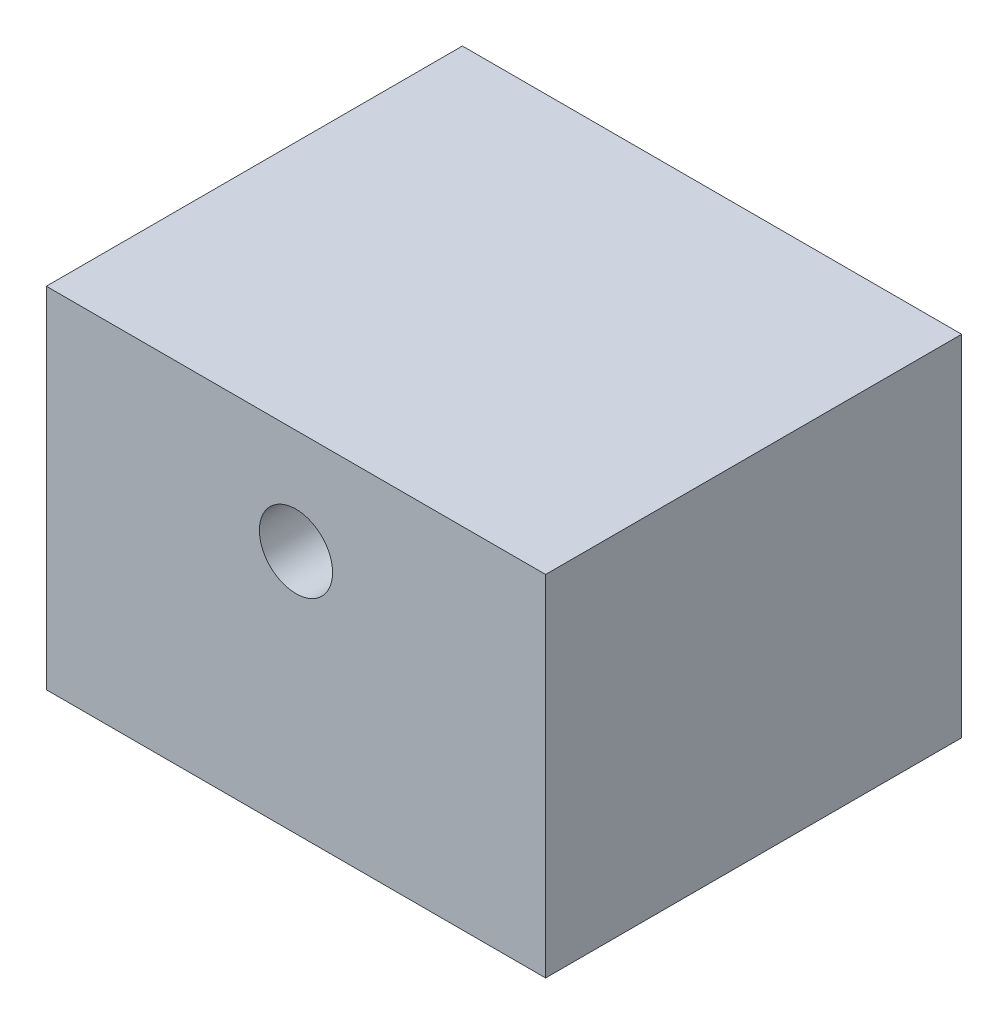
SolidWorks part; units mm, degrees
material "ABS PC"
ref_plane "Front Plane" through (0, 0, 0) normal (0, 0, 1) x (1, 0, 0)
ref_plane "Top Plane" through (0, 0, 0) normal (0, 1, 0) x (1, 0, 0)
ref_plane "Right Plane" through (0, 0, 0) normal (1, 0, 0) x (0, 0, -1)
sketch "Sketch1" plane through (0, 0, 0) normal (0, 0, 1) x (1, 0, 0)
  line L1 (0, 0) -> (30, 0)
  line L2 (0, 0) -> (0, 21)
  line L3 (0, 21) -> (30, 21)
  line L4 (30, 0) -> (30, 21)
  circle A0 centre (15, 14.7) radius 2.2
  point P7 (15, 0)
  dimension "D3" = 4.4
  dimension "D1" = 21
  dimension "D2" = 30
  dimension "D4" = 14.7
extrude "Boss-Extrude1" add sketch "Sketch1" along normal mid plane 25
